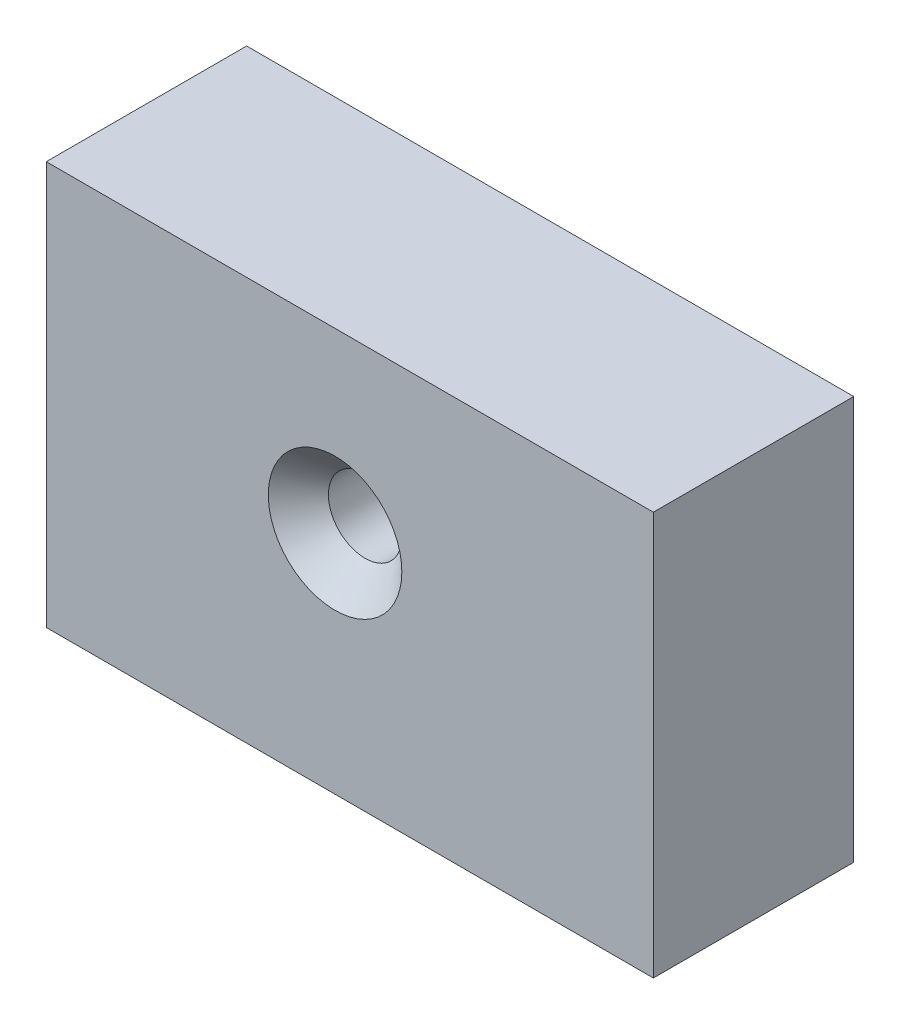
SolidWorks part; units mm, degrees
ref_plane "Front Plane" through (0, 0, 0) normal (0, 0, 1) x (1, 0, 0)
ref_plane "Top Plane" through (0, 0, 0) normal (0, 1, 0) x (1, 0, 0)
ref_plane "Right Plane" through (0, 0, 0) normal (1, 0, 0) x (0, 0, -1)
sketch "Sketch1" plane through (0, 0, 0) normal (0, 0, 1) x (1, 0, 0)
  line L1 (-29.1205, 26.5627) -> (61.7828, 26.5627)
  line L2 (-29.1205, 26.5627) -> (-29.1205, -33.8428)
  line L3 (-29.1205, -33.8428) -> (61.7828, -33.8428)
  line L4 (61.7828, 26.5627) -> (61.7828, -33.8428)
extrude "Boss-Extrude1" add sketch "Sketch1" along normal blind 30
hole_wizard "CSK for M10 Countersunk Flat Head Screw1" positions "Sketch2" profile "Sketch3" countersink size "M10" standard "DIN"
sketch "Sketch2" plane through (0, 0, 30) normal (0, 0, 1) x (1, 0, 0)
  point P0 (14.1202, 0)
sketch "Sketch3" plane through (14.1202, 0, 30) normal (1, 0, 0) x (0, -1, 0)
  line L0 (0, 0) -> (0, 28.3047)
  line L1 (0, 28.3047) -> (5.5, 25)
  line L2 (5.5, 25) -> (5.5, 4.5)
  line L3 (5.5, 4.5) -> (10, 0)
  line L5 (10, 0) -> (0, 0)
  line L6 (-5.5, 4.5) -> (-10, 0) construction
  line L10 (0, 28.3047) -> (-5.5, 25) construction
  line L11 (0, -6.35) -> (0, 107.95) construction
  dimension "Hole Dia." = 11
  dimension "Hole Depth" = 25
  dimension "Near C'Sink Dia." = 20
  dimension "Near C'Sink Angle" = 90
  dimension "Drill Angle" = 118
